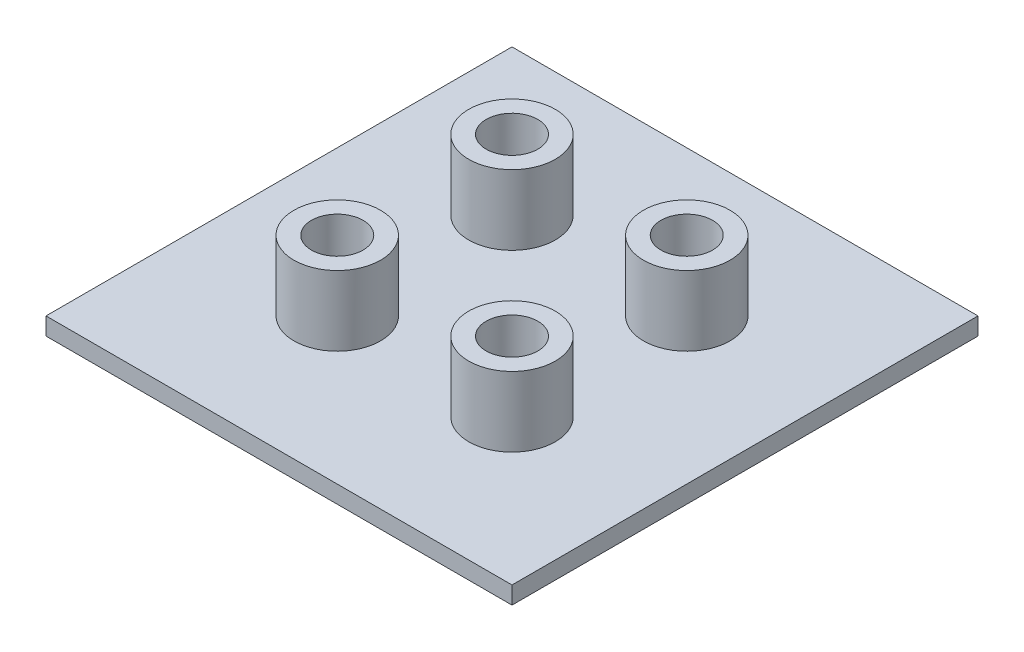
SolidWorks part; units mm, degrees
ref_plane "Front Plane" through (0, 0, 0) normal (0, 0, 1) x (1, 0, 0)
ref_plane "Top Plane" through (0, 0, 0) normal (0, 1, 0) x (1, 0, 0)
ref_plane "Right Plane" through (0, 0, 0) normal (1, 0, 0) x (0, 0, -1)
sketch "Sketch1" plane through (0, 0, 0) normal (0, 1, 0) x (1, 0, 0)
  line L1 (-40, -40) -> (40, -40)
  line L2 (-40, -40) -> (-40, 40)
  line L3 (-40, 40) -> (40, 40)
  line L4 (40, -40) -> (40, 40)
  line L5 (-40, -40) -> (40, 40) construction
  line L6 (-40, 40) -> (40, -40) construction
  point P0 (0, 0)
  dimension "D1" = 80
  dimension "D2" = 80
extrude "Boss-Extrude1" add sketch "Sketch1" along normal blind 3
sketch "Sketch2" plane through (0, 3, 0) normal (0, 1, 0) x (1, 0, 0)
  line L0 (0, 0) -> (-15, -15) construction
  line L1 (0, 0) -> (0, -26.2369) construction
  line L2 (-15, -15) -> (0, -15) construction
  line L3 (0, -15) -> (0, 0) construction
  circle A0 centre (-15, -15) radius 4.435
  circle A1 centre (-15, -15) radius 7.435
  dimension "D1" = 3
  dimension "D2" = 8.87
  dimension "D3" = 15
  dimension "D4" = 45
extrude "Boss-Extrude2" add sketch "Sketch2" along normal blind 12
ref_plane "Plane1" through (0, 0, 0) normal (0, 0, 1) x (1, 0, 0)
mirror "Mirror1" about plane through (0, 0, 0) normal (0, 0, 1) of "Boss-Extrude2"
ref_plane "Plane2" through (0, 0, 0) normal (1, 0, 0) x (0, 0, -1)
mirror "Mirror2" about plane through (0, 0, 0) normal (1, 0, 0) of "Mirror1", "Boss-Extrude2"
